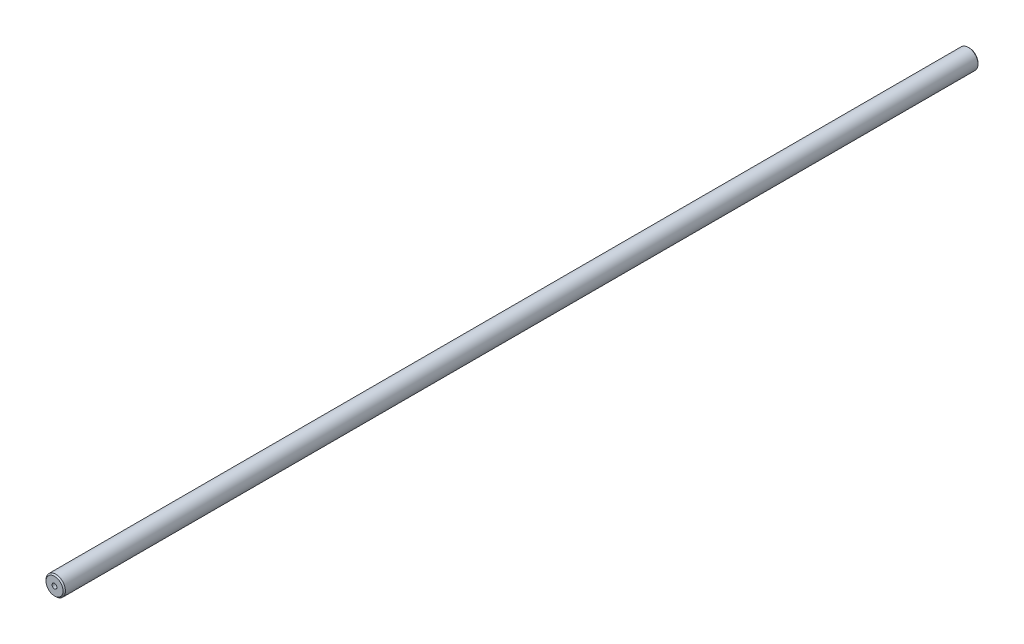
SolidWorks part; units mm, degrees
ref_plane "Front Plane" through (0, 0, 0) normal (0, 0, 1) x (1, 0, 0)
ref_plane "Top Plane" through (0, 0, 0) normal (0, 1, 0) x (1, 0, 0)
ref_plane "Right Plane" through (0, 0, 0) normal (1, 0, 0) x (0, 0, -1)
sketch "Sketch1" plane through (0, 0, 0) normal (0, 0, 1) x (1, 0, 0)
  circle A0 centre (0, 0) radius 4
  dimension "D1" = 8
extrude "Boss-Extrude1" add sketch "Sketch1" along normal blind 376
sketch "Sketch2" plane through (0, 0, 376) normal (0, 0, 1) x (1, 0, 0)
  circle A0 centre (0, 0) radius 1
  dimension "D1" = 2
extrude "Cut-Extrude1" cut sketch "Sketch2" against normal blind 10
chamfer "Chamfer1" distance 0.5 angle 45 2 edges at (4, 0, 0) (4, 0, 376)
